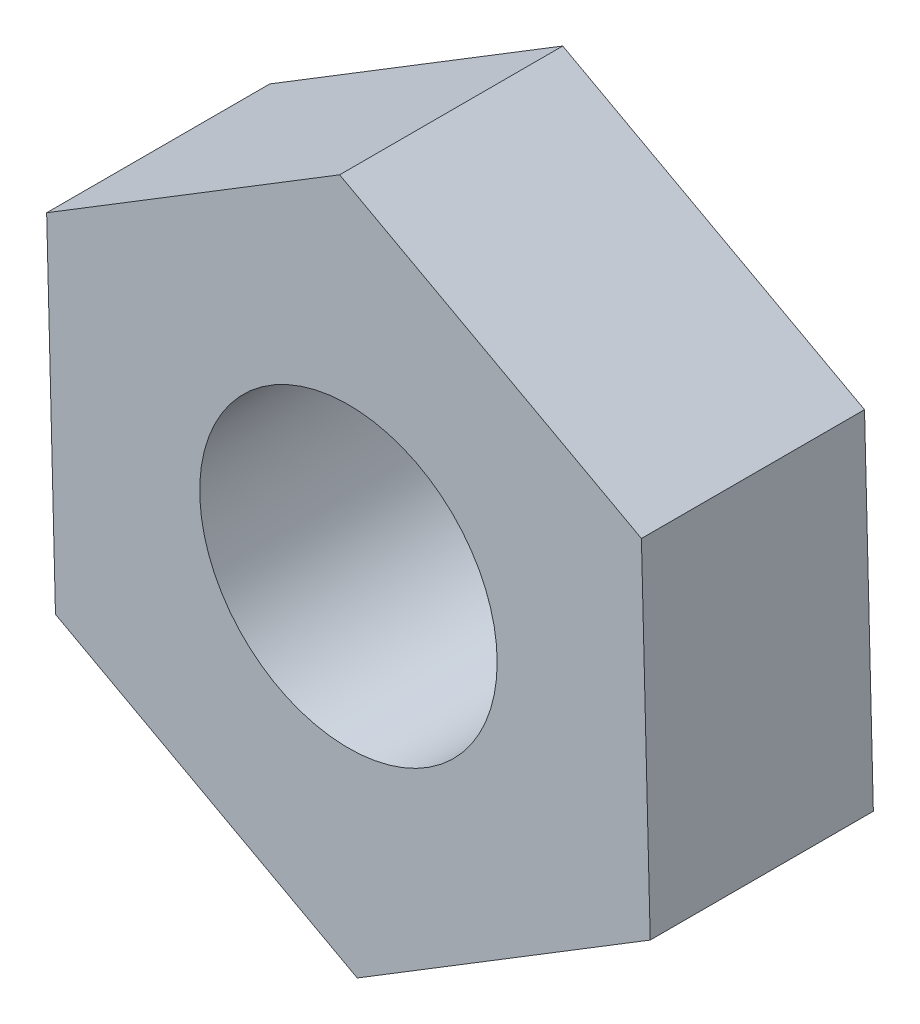
SolidWorks part; units mm, degrees
ref_plane "前视基准面" through (0, 0, 0) normal (0, 0, 1) x (1, 0, 0)
ref_plane "上视基准面" through (0, 0, 0) normal (0, 1, 0) x (1, 0, 0)
ref_plane "右视基准面" through (0, 0, 0) normal (1, 0, 0) x (0, 0, -1)
sketch "草图1" plane through (0, 0, 0) normal (0, 0, 1) x (1, 0, 0)
  line L1 (2.029, -1.103) -> (1.9697, 1.2056)
  line L2 (1.9697, 1.2056) -> (-0.0593, 2.3086)
  line L3 (-0.0593, 2.3086) -> (-2.029, 1.103)
  line L4 (-2.029, 1.103) -> (-1.9697, -1.2056)
  line L5 (-1.9697, -1.2056) -> (0.0593, -2.3086)
  line L6 (0.0593, -2.3086) -> (2.029, -1.103)
  circle A0 centre (0, 0) radius 2 construction
  dimension "D1" = 4
extrude "凸台-拉伸1" add sketch "草图1" along normal blind 1.5
sketch "草图2" plane through (0, 0, 1.5) normal (0, 0, 1) x (1, 0, 0)
  line L6 (0.0593, -2.3086) -> (2.029, -1.103)
  line L7 (2.029, -1.103) -> (1.9697, 1.2056)
  line L8 (1.9697, 1.2056) -> (-0.0593, 2.3086)
  line L9 (-0.0593, 2.3086) -> (-2.029, 1.103)
  line L10 (-2.029, 1.103) -> (-1.9697, -1.2056)
  line L11 (-1.9697, -1.2056) -> (0.0593, -2.3086)
  line L12 (0.0593, -2.3086) -> (2.029, -1.103)
  line L13 (2.029, -1.103) -> (1.9697, 1.2056)
  line L14 (1.9697, 1.2056) -> (-0.0593, 2.3086)
  line L15 (-0.0593, 2.3086) -> (-2.029, 1.103)
  line L16 (-2.029, 1.103) -> (-1.9697, -1.2056)
  line L17 (-1.9697, -1.2056) -> (0.0593, -2.3086)
  circle A0 centre (0, 0) radius 1
  dimension "D2" = 2
  dimension "D1" = 0
extrude "切除-拉伸1" cut sketch "草图2" against normal blind 2 contours A0
